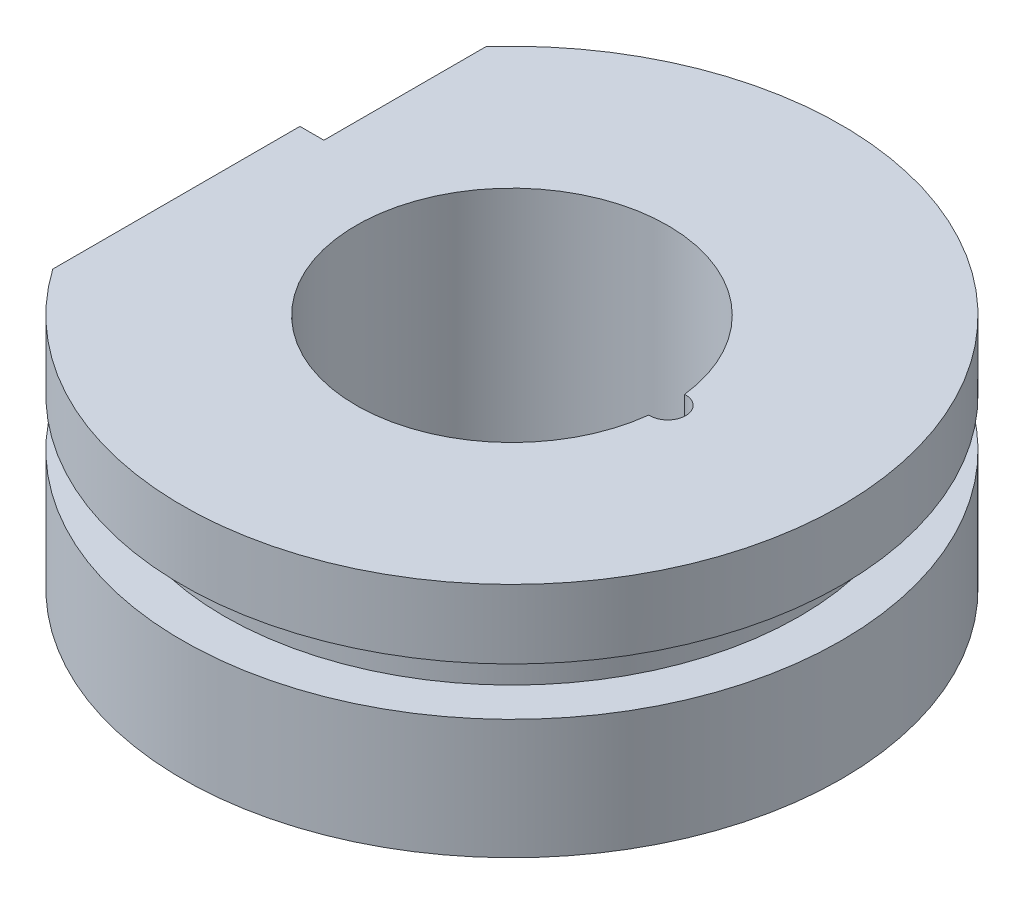
SolidWorks part; units mm, degrees
material "АЛ8Т4 ГОСТ 1583-93"
ref_plane "Спереди" through (0, 0, 0) normal (0, 0, 1) x (1, 0, 0)
ref_plane "Сверху" through (0, 0, 0) normal (0, 1, 0) x (1, 0, 0)
ref_plane "Справа" through (0, 0, 0) normal (1, 0, 0) x (0, 0, -1)
sketch "Эскиз1" plane through (0, 0, 0) normal (0, 1, 0) x (1, 0, 0)
  line L0 (-22.5, 15.8114) -> (-22.5, -15.8114)
  arc A0 (-22.5, -15.8114) -> (-22.5, 15.8114) centre (0, 0) ccw
  point P5 (27.5, 0)
  dimension "D1" = 55
  dimension "D2" = 50
extrude "Бобышка-Вытянуть1" add sketch "Эскиз1" along normal blind 19.75
sketch "Эскиз2" plane through (0, 0, 0) normal (0, 1, 0) x (1, 0, 0)
  circle A0 centre (0, 0) radius 13
  dimension "D1" = 26
extrude "Вырез-Вытянуть2" cut sketch "Эскиз2" along normal through all
sketch "Эскиз3" plane through (0, 0, 0) normal (1, 0, 0) x (0, 0, -1)
  line L0 (0, 0) -> (0, 19.75) construction
  line L1 (-29, 14) -> (-24, 14)
  line L2 (-29, 14) -> (-29, 10)
  line L3 (-29, 10) -> (-24, 10)
  line L4 (-24, 14) -> (-24, 10)
  line L5 (27.5, 19.75) -> (-27.5, 19.75) construction
  dimension "D1" = 10
  dimension "D2" = 4
  dimension "D3" = 24
  dimension "D4" = 5
revolve "Вырез-Повернуть1" cut sketch "Эскиз3" angle 360 about L0
sketch "Эскиз4" plane through (0, 0, 0) normal (0, 1, 0) x (1, 0, 0)
  circle A0 centre (13, 0) radius 1.5
  circle A1 centre (0, 0) radius 13 construction
  dimension "D1" = 3
extrude "Вырез-Вытянуть3" cut sketch "Эскиз4" along normal through all
ref_plane "Плоскость1" through (0, 0, -4.81) normal (0, 0, 1) x (1, 0, 0)
sketch "Эскиз5" plane through (0, 0, -4.81) normal (0, 0, 1) x (1, 0, 0)
  line L0 (-22.5, 19.75) -> (-20.5, 19.75)
  line L1 (27.5, 19.75) -> (-22.5, 19.75) construction
  line L2 (-20.5, 19.75) -> (-22.5, 17.75)
  line L3 (-22.5, 19.75) -> (-22.5, 14) construction
  line L4 (-22.5, 17.75) -> (-22.5, 19.75)
  dimension "D1" = 2
  dimension "D2" = 2
extrude "Вырез-Вытянуть4" cut sketch "Эскиз5" against normal through all
